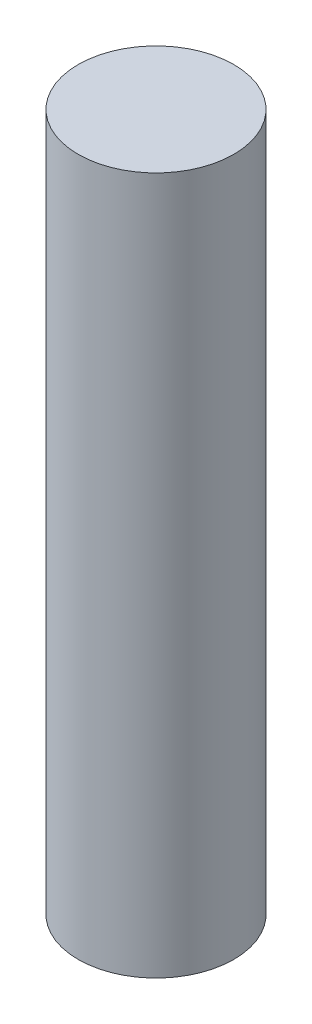
SolidWorks part; units mm, degrees
ref_plane "Front Plane" through (0, 0, 0) normal (0, 0, 1) x (1, 0, 0)
ref_plane "Top Plane" through (0, 0, 0) normal (0, 1, 0) x (1, 0, 0)
ref_plane "Right Plane" through (0, 0, 0) normal (1, 0, 0) x (0, 0, -1)
sketch "Sketch1" plane through (0, 0, 0) normal (0, 1, 0) x (1, 0, 0)
  line L0 (-0.75, 0) -> (0.75, 0) construction
  circle A0 centre (0, 0) radius 1.116
  point P6 (-0.5607, 26.4206)
  dimension "D2" = 2.2321
  dimension "D1" = 1.5
  dimension "D3" = 0.75
extrude "Boss-Extrude1" add sketch "Sketch1" along normal blind 10
